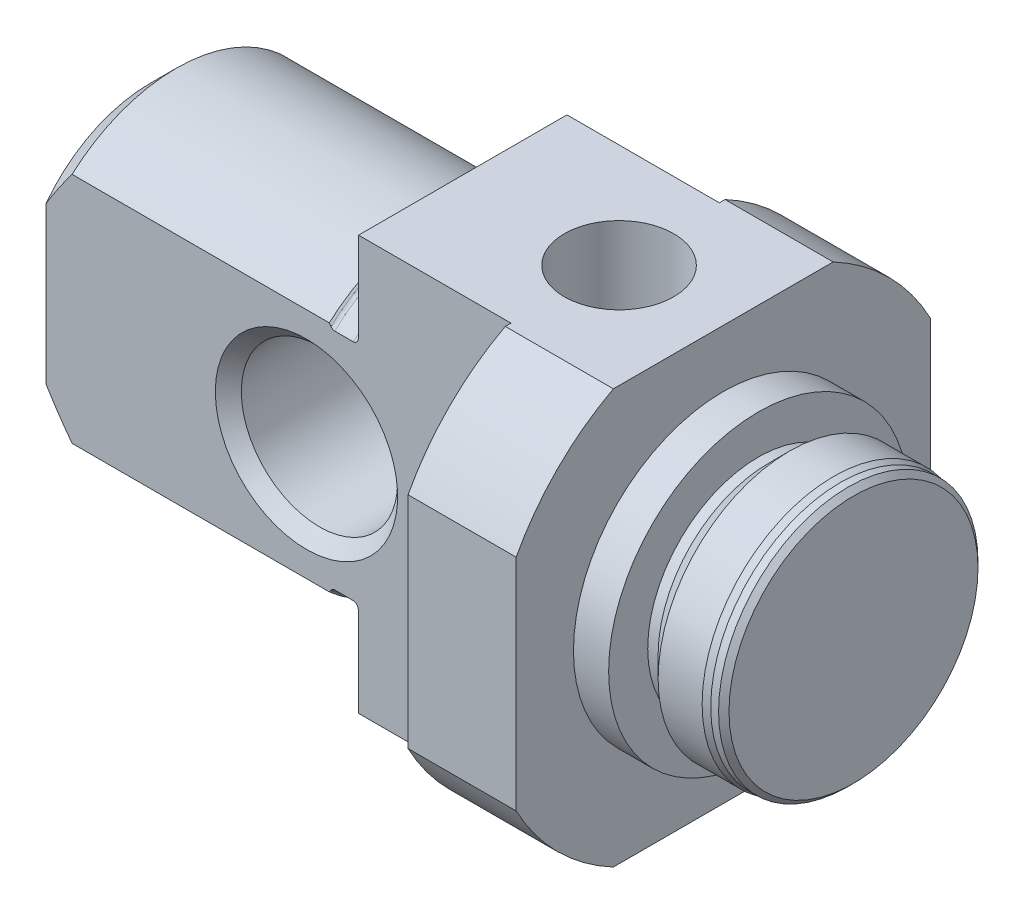
SolidWorks part; units mm, degrees
ref_plane "Front Plane" through (0, 0, 0) normal (0, 0, 1) x (1, 0, 0)
ref_plane "Top Plane" through (0, 0, 0) normal (0, 1, 0) x (1, 0, 0)
ref_plane "Right Plane" through (0, 0, 0) normal (1, 0, 0) x (0, 0, -1)
sketch "Sketch1" plane through (0, 0, 0) normal (0, 0, 1) x (1, 0, 0)
  line L0 (0, 0) -> (10860.2911, 0) construction
  line L1 (0, 0) -> (0, 10860.2911) construction
  line L2 (-22, 0) -> (-22, 5)
  line L3 (-21, 6) -> (-11.125, 6)
  line L4 (-11.125, 6) -> (-11.0586, 5.9336)
  line L5 (-10.9172, 5.875) -> (-10.2, 5.875)
  line L6 (-10, 6.075) -> (-10, 9)
  line L7 (-10, 9) -> (0, 9)
  line L8 (0, 9) -> (0, 5.75)
  line L9 (0, 5.75) -> (1.35, 5.75)
  line L10 (1.35, 5.75) -> (1.35, 4.25)
  line L11 (1.35, 4.25) -> (1.75, 4.25)
  line L12 (1.75, 4.25) -> (2.55, 5.05)
  line L13 (2.55, 5.05) -> (4.2388, 5.05)
  line L14 (4.2388, 5.05) -> (4.5, 4.98)
  line L15 (4.5, 4.98) -> (4.8, 4.98)
  line L16 (5, 4.78) -> (5, 0)
  line L17 (5, 0) -> (-22, 0)
  line L18 (4.8, 4.98) -> (5, 4.78)
  line L19 (-22, 5) -> (-21, 6)
  arc A0 (-10.2, 5.875) -> (-10, 6.075) centre (-10.2, 6.075) ccw
  arc A1 (-11.0586, 5.9336) -> (-10.9172, 5.875) centre (-10.9172, 6.075) ccw
  point P6 (-22, 6)
  point P20 (5, 4.98)
  point P27 (-10, 5.875)
  point P30 (-11, 5.875)
  dimension "AB-R" = 0.2
  dimension "I-Ø1" = 8.5
  dimension "E-Ø2" = 9.96
  dimension "E-Ø1" = 10.1
  dimension "O-Ø2" = 11.5
  dimension "O-Ø1" = 18
  dimension "T-Ø1" = 12
  dimension "L" = 27
  dimension "T-L" = 12
  dimension "A" = 0.4
  dimension "B2" = 3.65
  dimension "B1" = 5
  dimension "AB" = 1
  dimension "D13" = 45
  dimension "B3" = 0.5
  dimension "D15" = 15
  dimension "T-Ø2" = 11.75
  dimension "D17" = 45
  dimension "C-L2" = 0.2
  dimension "D19" = 45
  dimension "C-L1" = 1
  dimension "D21" = 45
revolve "Revolve1" add sketch "Sketch1" angle 360 about L0
cosmetic thread "Cosmetic Thread1" parameters "D2"=6.619
sketch "Sketch2" plane through (-10, 0, 0) normal (-1, 0, 0) x (0, 0, 1)
  line L0 (0, 0) -> (0, -50000) construction
  line L1 (-4.025, 7) -> (4.025, 7)
  line L2 (-4.225, 6.8) -> (-4.225, 7.9467)
  line L4 (4.225, 6.8) -> (4.225, 7.9467)
  circle A0 centre (0, 0) radius 9 construction
  arc A1 (4.225, 7.9467) -> (-4.225, 7.9467) centre (0, 0) ccw
  arc A2 (4.025, 7) -> (4.225, 6.8) centre (4.025, 6.8) cw
  arc A3 (-4.025, 7) -> (-4.225, 6.8) centre (-4.025, 6.8) ccw
  dimension "M-R1" = 0.2
  dimension "M-L" = 16
  dimension "M1" = 8.45
extrude "Boss-Extrude1" [suppressed] add sketch "Sketch2" against normal up to surface (15.5 mm away)
sketch "Sketch3" plane through (-22, 0, 0) normal (-1, 0, 0) x (0, 0, 1)
  line L0 (-4, 8.0623) -> (-4, -8.0623)
  line L1 (4, 8.0623) -> (4, -8.0623)
  line L2 (0, 0) -> (0, 18.183) construction
  arc A0 (4, -8.0623) -> (4, 8.0623) centre (0, 0) ccw
  circle A3 centre (0, 0) radius 9 construction
  arc A4 (-4, 8.0623) -> (-4, -8.0623) centre (0, 0) ccw
  dimension "X" = 8
extrude "O-L" cut sketch "Sketch3" against normal offset from surface (17.85 mm away) 5.5 up to face at (1.35, 0, 5.75)
sketch "Sketch6" plane through (-10, 0, 0) normal (-1, 0, 0) x (0, 0, 1)
  line L0 (0, 0) -> (0, 50000) construction
  line L1 (0, 0) -> (50000, 0) construction
  line L2 (-4.2187, 7.95) -> (4.2187, 7.95)
  line L3 (7.95, 4.2187) -> (7.95, -4.2187)
  line L4 (4.2187, -7.95) -> (-4.2187, -7.95)
  line L5 (-7.95, -4.2187) -> (-7.95, 4.2187)
  circle A0 centre (0, 0) radius 9 construction
  arc A1 (-7.95, 4.2187) -> (-7.95, -4.2187) centre (0, 0) ccw
  arc A2 (4.2187, 7.95) -> (-4.2187, 7.95) centre (0, 0) ccw
  arc A3 (7.95, -4.2187) -> (7.95, 4.2187) centre (0, 0) ccw
  arc A4 (-4.2187, -7.95) -> (4.2187, -7.95) centre (0, 0) ccw
  point P20 (0, 0)
  dimension "D1" = 15.9
  dimension "D2" = 4
extrude "Cut-Extrude4" cut sketch "Sketch6" against normal up to next
sketch "Sketch4" plane through (0, 0, 4) normal (0, 0, 1) x (1, 0, 0)
  line L0 (1.35, -5.75) -> (1.35, 5.75) construction
  circle A0 centre (-12, 0) radius 3
  dimension "ØN" = 6
  dimension "N-L" = 13.35
extrude "Cut-Extrude2" cut sketch "Sketch4" against normal up to next
chamfer "Chamfer4" distance 0.5 angle 45 2 edges at (-9, 0, -4) (-9, 0, 4)
hole_wizard "M5 Tapped Hole1" positions "Sketch7" profile "Sketch8" tap size "M5" standard "ISO"
sketch "Sketch7" plane through (0, 7.95, 0) normal (0, 1, 0) x (1, 0, 0)
  line L0 (0, 0) -> (-5.5462, 0) construction
  line L2 (0, -4.2187) -> (0, 4.2187) construction
  point P0 (-4, 0)
  dimension "D1" = 4
sketch "Sketch8" plane through (-4, 7.95, 0) normal (1, 0, 0) x (0, 0, 1)
  line L0 (0, 0) -> (0, 7.2124)
  line L1 (0, 7.2124) -> (2.1, 6)
  line L2 (2.1, 6) -> (2.1, 0)
  line L5 (2.1, 0) -> (0, 0)
  line L10 (0, 7.2124) -> (-2.1, 6) construction
  line L11 (0, -6.35) -> (0, 107.95) construction
  dimension "Tap Drill Dia." = 4.2
  dimension "Tap Drill Depth" = 6
  dimension "Drill Angle" = 120
cosmetic thread "Hole Thread1" parameters "D1"=5, "D2"=5
hole_wizard "M5 Tapped Hole2" [suppressed] positions "Sketch9" profile "Sketch10" tap size "M5" standard "IS"
sketch "Sketch9" plane through (0, 10.5, 0) normal (0, 1, 0) x (1, 0, 0)
  line L0 (0, 0) -> (-9.5002, 0) construction
  line L2 (0, 4.55) -> (0, -4.55) construction
  point P0 (-5.35, 0)
  dimension "D1" = 5.35
sketch "Sketch10" plane through (-5.35, 10.5, 0) normal (1, 0, 0) x (0, 0, 1)
  line L0 (0, 0) -> (0, 8.2124)
  line L1 (0, 8.2124) -> (2.1, 7)
  line L2 (2.1, 7) -> (2.1, 0)
  line L5 (2.1, 0) -> (0, 0)
  line L10 (0, 8.2124) -> (-2.1, 7) construction
  line L11 (0, -6.35) -> (0, 107.95) construction
  dimension "Tap Drill Dia." = 4.2
  dimension "Tap Drill Depth" = 7
  dimension "Drill Angle" = 120
cosmetic thread "Hole Thread2" [suppressed] parameters "D1"=6.5, "D2"=5
hole_wizard "G1/8 Tapped Hole1" [suppressed] positions "Sketch11" profile "Sketch12" tap size "G1/8" standard "IS"
sketch "Sketch11" plane through (0, 15.5, 0) normal (0, 1, 0) x (1, 0, 0)
  line L0 (0, 0) -> (-7.5, 0) construction
  line L2 (0, 6.8) -> (0, -6.8) construction
  point P0 (-7.5, 0)
  dimension "D1" = 7.5
sketch "Sketch12" plane through (-7.5, 15.5, 0) normal (1, 0, 0) x (0, 0, 1)
  line L0 (0, 0) -> (0, 11.6438)
  line L1 (0, 11.6438) -> (4.4, 9)
  line L2 (4.4, 9) -> (4.4, 0)
  line L5 (4.4, 0) -> (0, 0)
  line L10 (0, 11.6438) -> (-4.4, 9) construction
  line L11 (0, -6.35) -> (0, 107.95) construction
  dimension "Tap Drill Dia." = 8.8
  dimension "Tap Drill Depth" = 9
  dimension "Drill Angle" = 118
cosmetic thread "Hole Thread3" [suppressed] parameters "D1"=8.5, "D2"=9.728
